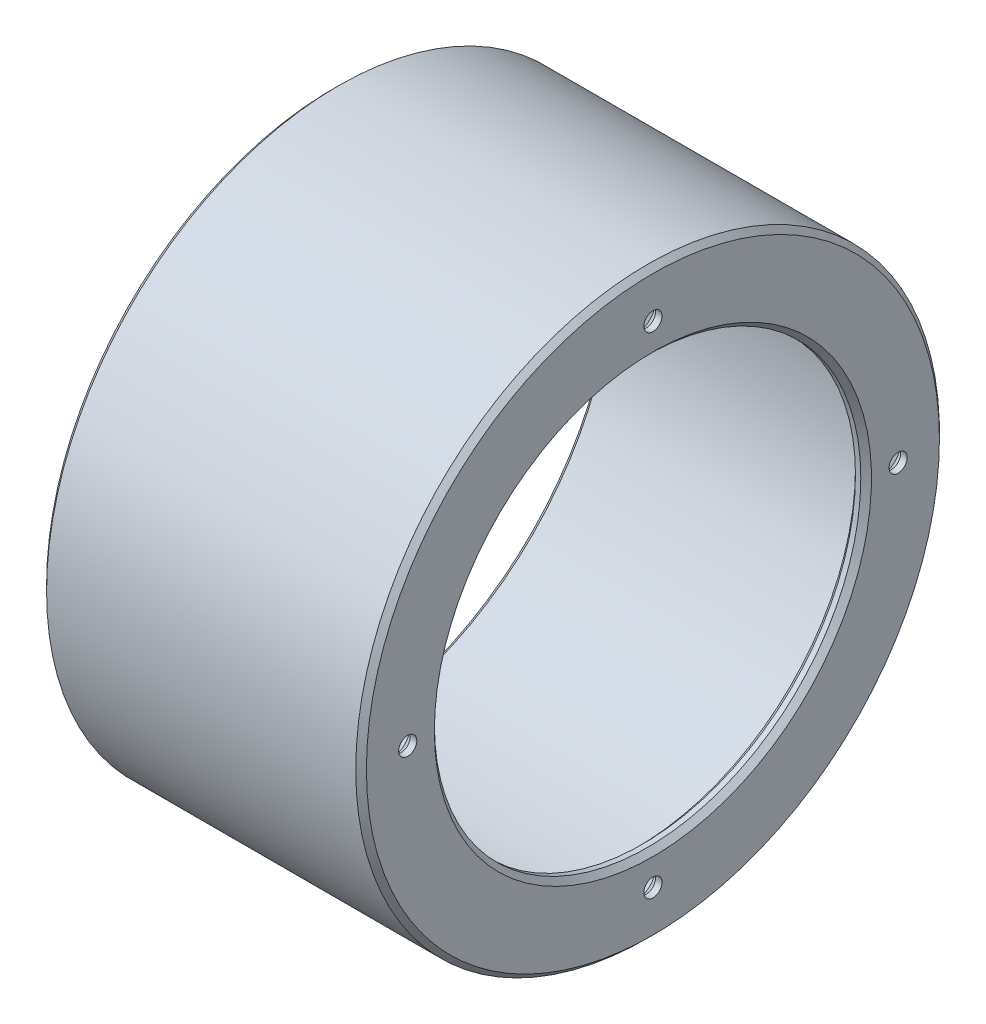
SolidWorks part; units mm, degrees
material "Сталь 40Х ГОСТ 4543-71"
ref_plane "Спереди (Плоскость XY)" through (0, 0, 0) normal (0, 0, 1) x (1, 0, 0)
ref_plane "Сверху (Плоскость XZ)" through (0, 0, 0) normal (0, 1, 0) x (1, 0, 0)
ref_plane "Справа (Плоскость ZY)" through (0, 0, 0) normal (1, 0, 0) x (0, 0, -1)
other "Configuration Table"
sketch "Эскиз1" plane through (0, 0, 0) normal (0, 0, 1) x (1, 0, 0)
  line L0 (0, 0) -> (96.7103, 0) construction
  line L1 (0, 54.75) -> (60, 54.75)
  line L2 (60, 54.75) -> (60, 40)
  line L3 (60, 40) -> (57, 40)
  line L4 (57, 40) -> (57, 51.5)
  line L5 (57, 51.5) -> (0, 51.5)
  line L6 (0, 51.5) -> (0, 54.75)
  point P9 (0, 0)
  dimension "D1" = 109.5
  dimension "D2" = 103
  dimension "D3" = 60
  dimension "D4" = 3
  dimension "D5" = 80
revolve "Повернуть1" add sketch "Эскиз1" angle 360 about L0
chamfer "Фаска1" distance 1 angle 45 5 edges at (60, 0, 54.75) (0, 0, 54.75) (60, 0, 40) (57, 0, 40) (0, 0, 51.5)
hole_wizard "Зенковка для винта с потайной головкой и внутренним шестигранником M31" positions "Эскиз6" profile "Эскиз5" countersink size "M3" standard "DIN"
sketch "Эскиз6" plane through (57, 0, 0) normal (-1, 0, 0) x (0, 0, 1)
  circle A0 centre (0, 0) radius 40 construction
  point P0 (0, 46)
  dimension "D1" = 46
sketch "Эскиз5" plane through (57, 46, 0) normal (0, 1, 0) x (0, 0, 1)
  line L0 (0, 0) -> (0, 22.5)
  line L1 (0, 22.5) -> (1.7, 21.4785)
  line L2 (1.7, 21.4785) -> (1.7, 1.77)
  line L3 (1.7, 1.77) -> (3.47, 0)
  line L5 (3.47, 0) -> (0, 0)
  line L6 (-1.7, 1.77) -> (-3.47, 0) construction
  line L10 (0, 22.5) -> (-1.7, 21.4785) construction
  line L11 (0, -6.35) -> (0, 107.95) construction
  dimension "Диаметр отверстия" = 3.4
  dimension "Глубина отверстия" = 22.5
  dimension "Диаметр передней зенковки" = 6.94
  dimension "Угол передней зенковки" = 90
  dimension "Угол заточки сверла" = 118
pattern_circular "Круговой массив2" count 4 over 360 about axis through (0, 0, 0) along (1, 0, 0) of "Зенковка для винта с потайной головкой и внутренним шестигранником M31"
